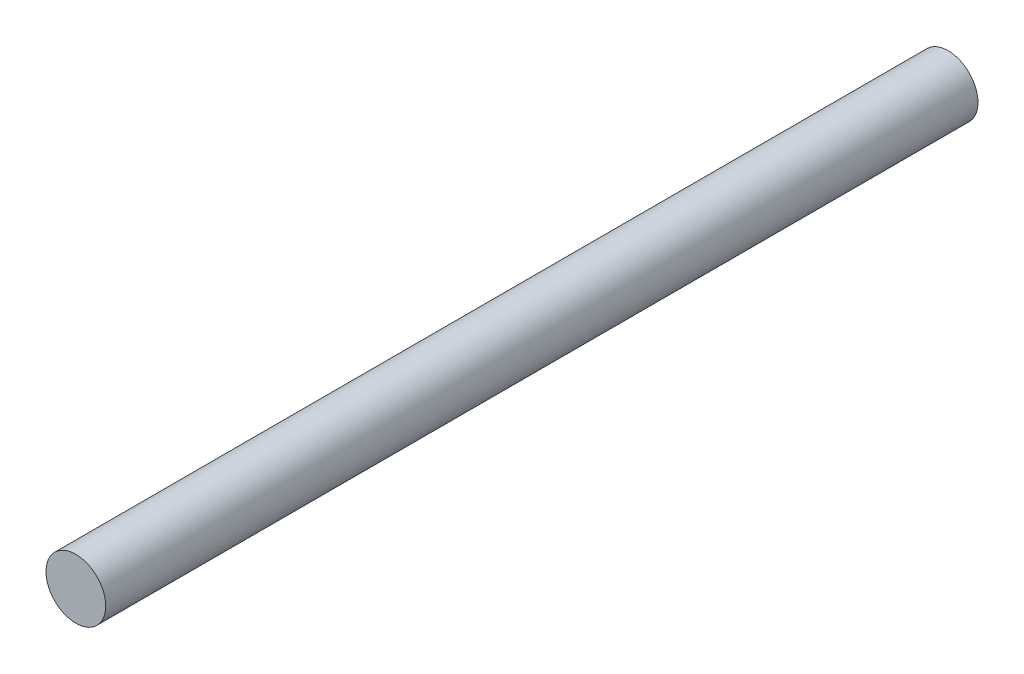
SolidWorks part; units mm, degrees
material "Plain Carbon Steel"
ref_plane "Front Plane" through (0, 0, 0) normal (0, 0, 1) x (1, 0, 0)
ref_plane "Top Plane" through (0, 0, 0) normal (0, 1, 0) x (1, 0, 0)
ref_plane "Right Plane" through (0, 0, 0) normal (1, 0, 0) x (0, 0, -1)
sketch "Sketch1" plane through (0, 0, 0) normal (0, 0, 1) x (1, 0, 0)
  circle A0 centre (0, 0) radius 2.5
  dimension "D1" = 5
extrude "Boss-Extrude1" add sketch "Sketch1" along normal blind 73
